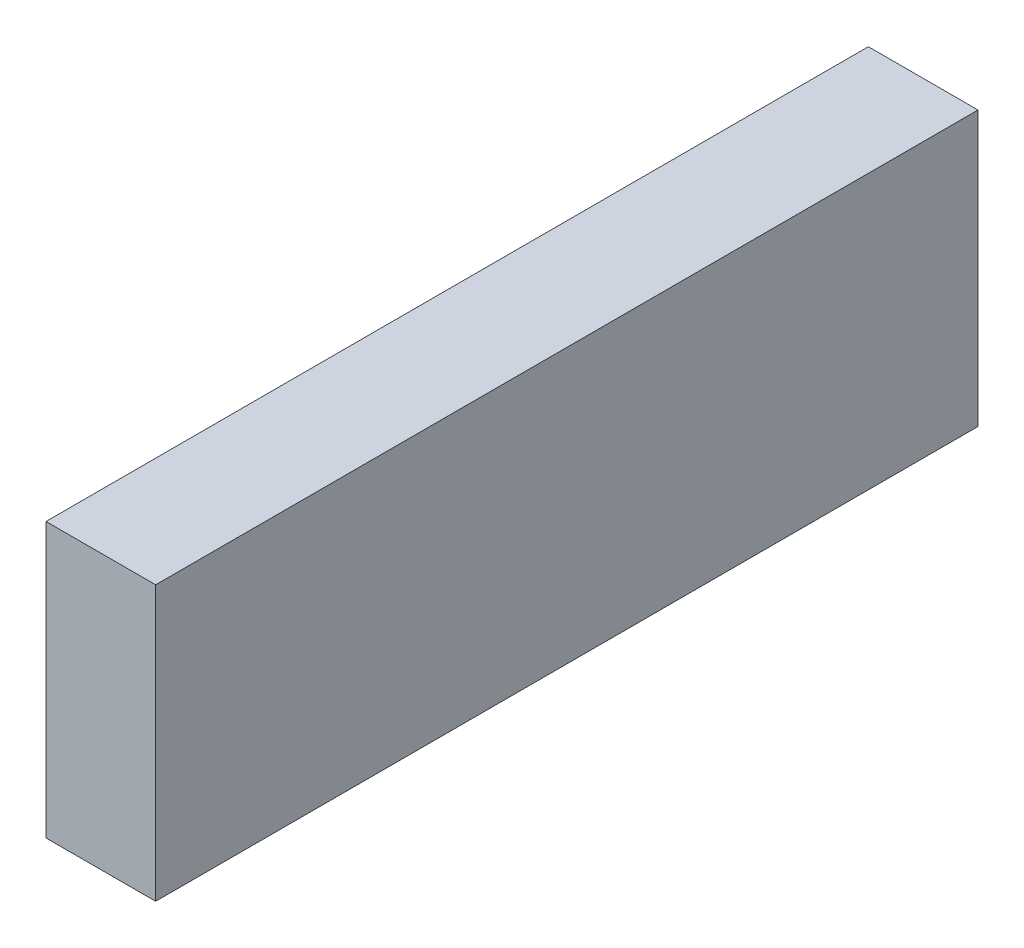
SolidWorks part; units mm, degrees
ref_plane "Front Plane" through (0, 0, 0) normal (0, 0, 1) x (1, 0, 0)
ref_plane "Top Plane" through (0, 0, 0) normal (0, 1, 0) x (1, 0, 0)
ref_plane "Right Plane" through (0, 0, 0) normal (1, 0, 0) x (0, 0, -1)
sketch "Sketch1" plane through (0, 0, 0) normal (1, 0, 0) x (0, 0, -1)
  line L1 (-150, 50) -> (150, 50)
  line L2 (-150, 50) -> (-150, -50)
  line L3 (-150, -50) -> (150, -50)
  line L4 (150, 50) -> (150, -50)
  line L5 (-150, 50) -> (150, -50) construction
  line L6 (-150, -50) -> (150, 50) construction
  point P0 (0, 0)
  dimension "D1" = 300
  dimension "D2" = 100
extrude "Boss-Extrude1" add sketch "Sketch1" along normal blind 40
